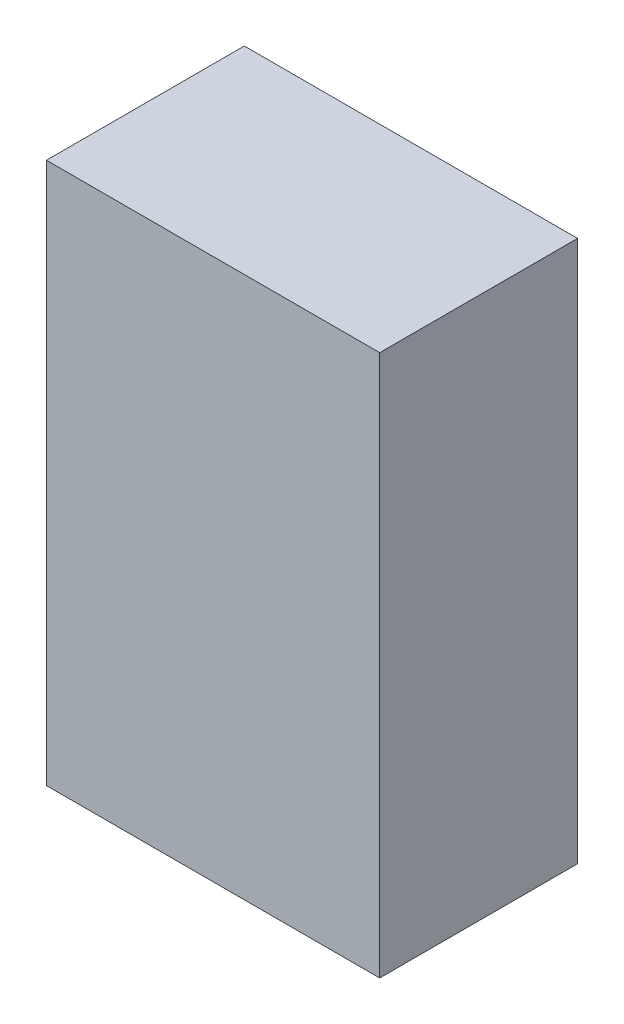
SolidWorks part; units mm, degrees
ref_plane "Front Plane" through (0, 0, 0) normal (0, 0, 1) x (1, 0, 0)
ref_plane "Top Plane" through (0, 0, 0) normal (0, 1, 0) x (1, 0, 0)
ref_plane "Right Plane" through (0, 0, 0) normal (1, 0, 0) x (0, 0, -1)
sketch "Sketch1" plane through (0, 0, 0) normal (0, 0, 1) x (1, 0, 0)
  line L1 (0, 0) -> (32, 0)
  line L2 (0, 0) -> (0, -52)
  line L3 (0, -52) -> (32, -52)
  line L4 (32, 0) -> (32, -52)
  dimension "D1" = 52
  dimension "D2" = 32
extrude "Boss-Extrude1" add sketch "Sketch1" along normal blind 19
